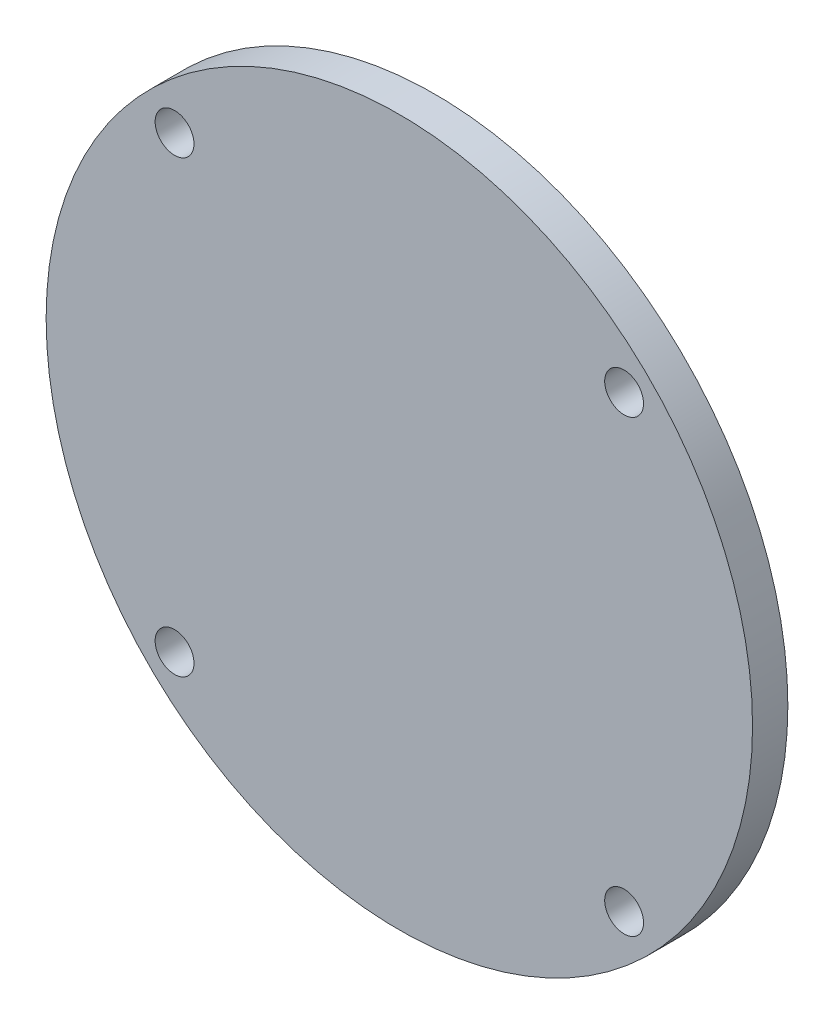
SolidWorks part; units mm, degrees
ref_plane "Front" through (0, 0, 0) normal (0, 0, 1) x (1, 0, 0)
ref_plane "Top" through (0, 0, 0) normal (0, 1, 0) x (1, 0, 0)
ref_plane "Right" through (0, 0, 0) normal (1, 0, 0) x (0, 0, -1)
sketch "Sketch1" plane through (0, 0, 0) normal (0, 0, 1) x (1, 0, 0)
  circle A0 centre (0, 0) radius 50
  dimension "D1" = 100
extrude "Extrude1" add sketch "Sketch1" against normal blind 5
hole_wizard "M5.5 (5.5) Diameter Hole2" positions "Sketch5" profile "Sketch4" hole size "M5.5" standard "Ansi Metric" end condition through all
sketch "Sketch5" plane through (0, 0, 0) normal (0, 0, 1) x (1, 0, 0)
  line L7 (-31.8198, 31.8198) -> (31.8198, 31.8198) construction
  line L8 (-31.8198, 31.8198) -> (-31.8198, -31.8198) construction
  line L9 (-31.8198, -31.8198) -> (31.8198, -31.8198) construction
  line L10 (31.8198, 31.8198) -> (31.8198, -31.8198) construction
  circle A0 centre (0, 0) radius 45 construction
  point P0 (-31.8198, 31.8198)
  point P1 (31.8198, 31.8198)
  point P3 (31.8198, -31.8198)
  point P5 (-31.8198, -31.8198)
  dimension "D1" = 90
sketch "Sketch4" plane through (-31.8198, 31.8198, 0) normal (1, 0, 0) x (0, -1, 0)
  line L0 (0, 0) -> (0, 5)
  line L1 (0, 5) -> (2.75, 5)
  line L2 (2.75, 5) -> (2.75, 0)
  line L5 (2.75, 0) -> (0, 0)
  line L11 (0, -6.35) -> (0, 107.95) construction
  dimension "Thru Hole Dia." = 5.5
  dimension "Thru Hole Depth" = 5
